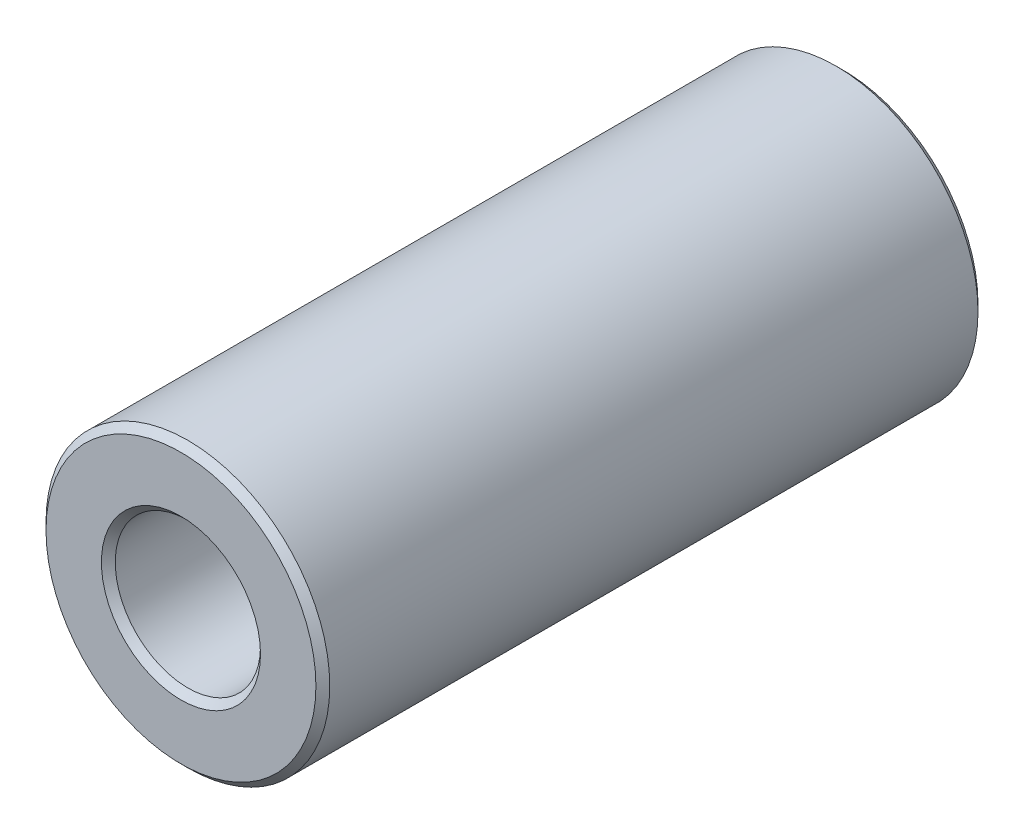
SolidWorks part; units mm, degrees
material "6061 Alloy"
ref_plane "Front Plane" through (0, 0, 0) normal (0, 0, 1) x (1, 0, 0)
ref_plane "Top Plane" through (0, 0, 0) normal (0, 1, 0) x (1, 0, 0)
ref_plane "Right Plane" through (0, 0, 0) normal (1, 0, 0) x (0, 0, -1)
sketch "Sketch1" plane through (0, 0, 0) normal (0, 0, 1) x (1, 0, 0)
  circle A0 centre (0, 0) radius 4.7625 construction
  circle A1 centre (0, 0) radius 2.4384 construction
  point P4 (0, 4.7625)
  dimension "ID" = 4.8768
  dimension "OD" = 9.525
sketch "Sketch2" plane through (0, 0, 0) normal (1, 0, 0) x (0, 0, -1)
  line L0 (-11.1125, 4.7625) -> (11.1125, 4.7625) construction
  dimension "Length" = 22.225
sketch "Sketch3" plane through (0, 0, 0) normal (0, 0, 1) x (1, 0, 0)
  circle A0 centre (0, 0) radius 2.4384 construction
  circle A1 centre (0, 0) radius 4.7625 construction
  circle A2 centre (0, 0) radius 2.4384
  circle A3 centre (0, 0) radius 4.7625
extrude "Boss-Extrude1" add sketch "Sketch3" against normal up to vertex (11.1125 mm away) and the other way up to vertex (11.1125 mm away) up to point (0, 4.7625, -11.1125) other way up to point (0, 4.7625, 11.1125)
chamfer "Chamfer1" distance 0.2324 angle 45 1 edges at (4.7625, 0, 11.1125)
equation "\"D1@Chamfer1\"=(\"OD@Sketch1\"-\"ID@Sketch1\")*0.05"
